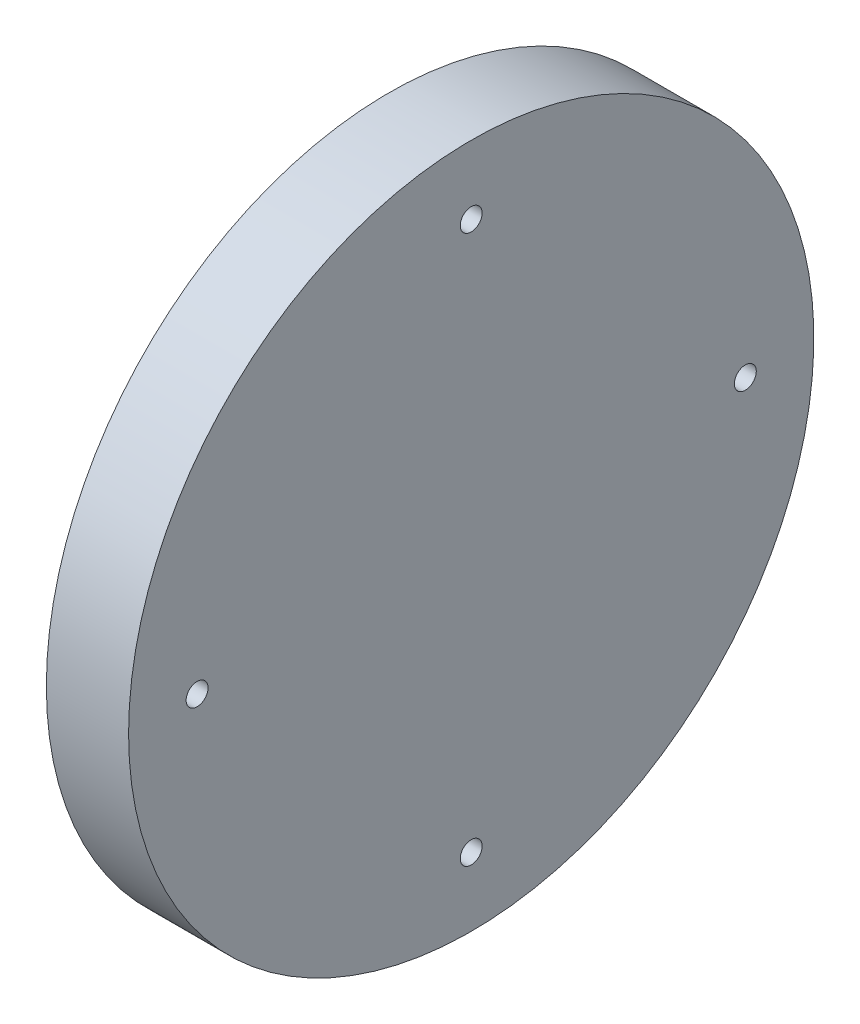
SolidWorks part; units mm, degrees
ref_plane "정면" through (0, 0, 0) normal (0, 0, 1) x (1, 0, 0)
ref_plane "윗면" through (0, 0, 0) normal (0, 1, 0) x (1, 0, 0)
ref_plane "우측면" through (0, 0, 0) normal (1, 0, 0) x (0, 0, -1)
ref_plane "평면1" through (0, 0, 0) normal (0, 0, -1) x (-1, 0, 0)
sketch "스케치1" plane through (0, 0, 0) normal (0, 0, -1) x (-1, 0, 0)
  line L0 (-11, 25) -> (-11, 0)
  line L1 (-11, 0) -> (-5, 0)
  line L2 (-5, 0) -> (-5, 25)
  line L3 (-5, 25) -> (-11, 25)
  line L4 (-11, 0) -> (-5, 0) construction
revolve "회전1" add sketch "스케치1" angle 360 about L4
sketch "스케치2" plane through (5, 0, 0) normal (-1, 0, 0) x (0, 0, 1)
  circle A0 centre (0, 0) radius 9.5
extrude "보스-돌출1" add sketch "스케치2" along normal blind 5
hole_wizard "Ø1.6 (1.6) 지름 구멍1" positions "스케치4" profile "스케치3" hole size "Ø1.6" standard "Ansi Metric"
sketch "스케치4" plane through (5, 0, 0) normal (-1, 0, 0) x (0, 0, 1)
  point P0 (0, 20)
  point P1 (-20, 0)
  point P2 (0, -20)
  point P3 (20, 0)
sketch "스케치3" plane through (5, 20, 0) normal (0, 1, 0) x (0, 0, 1)
  line L0 (0, 0) -> (0, 6)
  line L1 (0, 6) -> (0.8, 6)
  line L2 (0.8, 6) -> (0.8, 0)
  line L5 (0.8, 0) -> (0, 0)
  line L11 (0, -6.35) -> (0, 107.95) construction
  dimension "관통 구멍 지름" = 1.6
  dimension "관통 구멍 깊이" = 6
